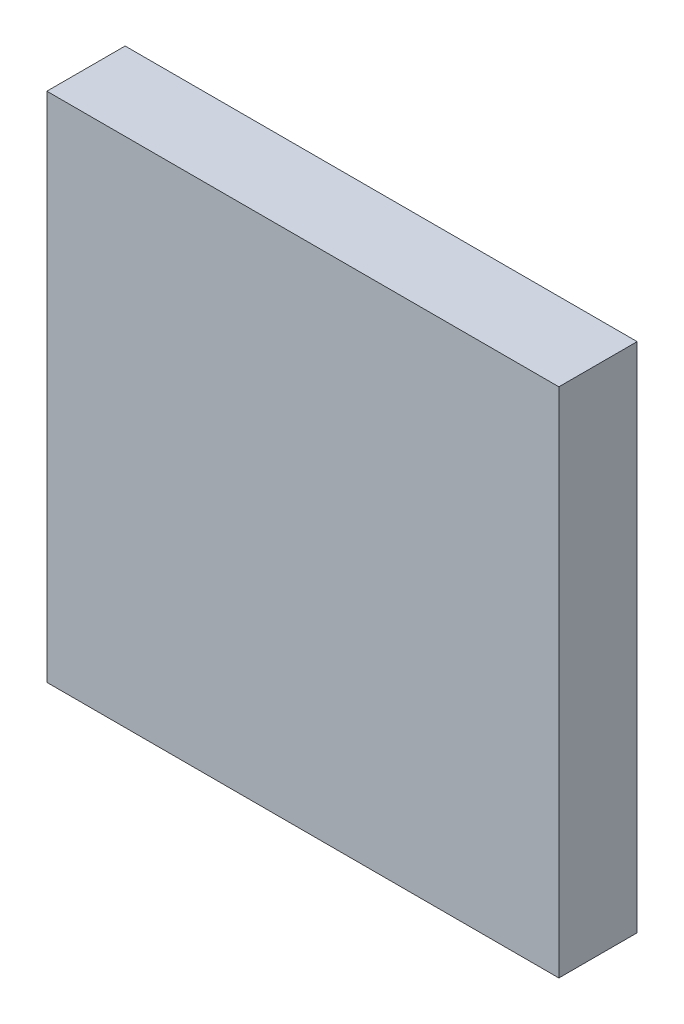
SolidWorks part; units mm, degrees
ref_plane "Спереди" through (0, 0, 0) normal (0, 0, 1) x (1, 0, 0)
ref_plane "Сверху" through (0, 0, 0) normal (0, 1, 0) x (1, 0, 0)
ref_plane "Справа" through (0, 0, 0) normal (1, 0, 0) x (0, 0, -1)
sketch "Эскиз1" plane through (0, 0, 0) normal (0, 0, 1) x (1, 0, 0)
  line L1 (-35, 35) -> (35, 35)
  line L2 (-35, 35) -> (-35, -35)
  line L3 (-35, -35) -> (35, -35)
  line L4 (35, 35) -> (35, -35)
  line L5 (-35, 35) -> (35, -35) construction
  line L6 (-35, -35) -> (35, 35) construction
  point P0 (0, 0)
extrude "Бобышка-Вытянуть1" add sketch "Эскиз1" against normal blind 10.7
sketch "Эскиз2" plane through (0, 0, -10.7) normal (0, 0, -1) x (-1, 0, 0)
  line L1 (-30.25, 30.25) -> (30.25, 30.25)
  line L2 (-30.25, 30.25) -> (-30.25, -30.25)
  line L3 (-30.25, -30.25) -> (30.25, -30.25)
  line L4 (30.25, 30.25) -> (30.25, -30.25)
  line L5 (-30.25, 30.25) -> (30.25, -30.25) construction
  line L6 (-30.25, -30.25) -> (30.25, 30.25) construction
  point P0 (0, 0)
extrude "Вырез-Вытянуть1" cut sketch "Эскиз2" against normal blind 9.2
